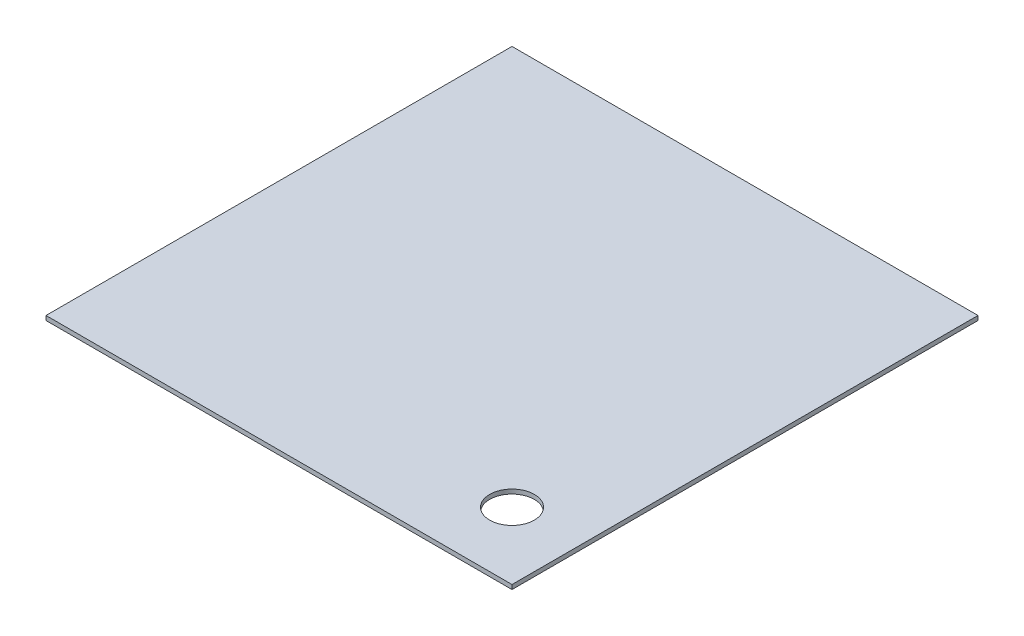
SolidWorks part; units mm, degrees
material "Cedar"
ref_plane "Front Plane" through (0, 0, 0) normal (0, 0, 1) x (1, 0, 0)
ref_plane "Top Plane" through (0, 0, 0) normal (0, 1, 0) x (1, 0, 0)
ref_plane "Right Plane" through (0, 0, 0) normal (1, 0, 0) x (0, 0, -1)
sketch "Sketch1" plane through (0, 0, 0) normal (0, 1, 0) x (1, 0, 0)
  line L1 (-132.6642, -132.6642) -> (132.6642, -132.6642)
  line L2 (-132.6642, -132.6642) -> (-132.6642, 132.6642)
  line L3 (-132.6642, 132.6642) -> (132.6642, 132.6642)
  line L4 (132.6642, -132.6642) -> (132.6642, 132.6642)
  line L5 (-132.6642, -132.6642) -> (132.6642, 132.6642) construction
  line L6 (-132.6642, 132.6642) -> (132.6642, -132.6642) construction
  point P0 (0, 0)
  dimension "D1" = 265.3284
extrude "Boss-Extrude1" add sketch "Sketch1" along normal blind 2.5
sketch "Sketch2" plane through (0, 2.5, 0) normal (0, 1, 0) x (1, 0, 0)
  line L0 (132.6642, -132.6642) -> (132.6642, 132.6642) construction
  line L1 (-132.6642, -132.6642) -> (132.6642, -132.6642) construction
  circle A0 centre (94.5642, -94.5642) radius 12.7
  dimension "D1" = 25.4
  dimension "D2" = 38.1
  dimension "D3" = 38.1
extrude "Cut-Extrude1" cut sketch "Sketch2" against normal through all
